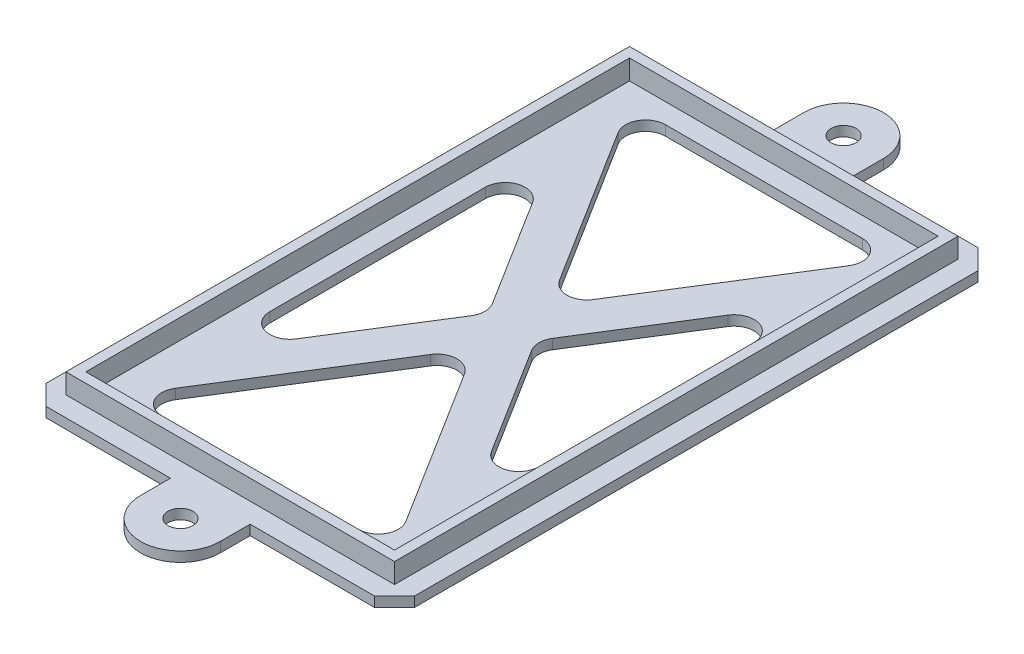
SolidWorks part; units mm, degrees
ref_plane "Front Plane" through (0, 0, 0) normal (0, 0, 1) x (1, 0, 0)
ref_plane "Top Plane" through (0, 0, 0) normal (0, 1, 0) x (1, 0, 0)
ref_plane "Right Plane" through (0, 0, 0) normal (1, 0, 0) x (0, 0, -1)
sketch "Sketch1" plane through (0, 0, 0) normal (0, 1, 0) x (1, 0, 0)
  line L8 (1.27, 1.27) -> (1.27, -70.612)
  line L9 (0, 0) -> (-39.37, 0)
  line L10 (0, 0) -> (0, -69.342)
  line L11 (0, -69.342) -> (-39.37, -69.342)
  line L12 (-39.37, 0) -> (-39.37, -69.342)
  line L13 (1.27, -70.612) -> (-40.64, -70.612)
  line L14 (-40.64, 1.27) -> (-40.64, -70.612)
  line L15 (1.27, 1.27) -> (-40.64, 1.27)
  dimension "D1" = 39.37
  dimension "D2" = 69.342
  dimension "D3" = 1.27
extrude "Boss-Extrude4" add sketch "Sketch1" along normal blind 2.54
sketch "Sketch5" plane through (0, 0, 0) normal (0, -1, 0) x (1, 0, 0)
  line L14 (-43.18, -3.81) -> (3.81, -3.81)
  line L15 (3.81, -3.81) -> (3.81, 73.152)
  line L16 (-43.18, 73.152) -> (-43.18, -3.81)
  line L17 (3.81, 73.152) -> (-43.18, 73.152)
  line L18 (-43.18, -3.81) -> (3.81, -3.81)
  line L19 (3.81, -3.81) -> (3.81, 73.152)
  line L20 (-43.18, 73.152) -> (-43.18, -3.81)
  line L21 (3.81, 73.152) -> (-43.18, 73.152)
  dimension "D1" = 2.54
extrude "Boss-Extrude5" add sketch "Sketch5" along normal blind 1.27
chamfer "Chamfer4" distance 2.54 angle 45 4 edges at (-43.18, -0.635, 73.152) (3.81, -0.635, 73.152) (3.81, -0.635, -3.81) (-43.18, -0.635, -3.81)
sketch "Sketch6" plane through (0, 0, 0) normal (0, 1, 0) x (1, 0, 0)
  line L0 (0, 0) -> (-39.37, 0) construction
  line L1 (-36.83, -2.54) -> (-2.54, -2.54)
  line L2 (-36.83, -12.1041) -> (-36.83, -57.2379)
  line L3 (-36.83, -66.802) -> (-2.54, -66.802)
  line L4 (-2.54, -12.1041) -> (-2.54, -57.2379)
  line L5 (0, -69.342) -> (0, 0) construction
  line L6 (-39.37, -69.342) -> (0, -69.342) construction
  line L7 (-39.37, 0) -> (-39.37, -69.342) construction
  line L8 (-36.83, -57.2379) -> (-22.6828, -34.671)
  line L9 (-2.54, -12.1041) -> (-16.6872, -34.671)
  line L10 (-36.83, -12.1041) -> (-22.6828, -34.671)
  line L11 (-36.83, -2.54) -> (-19.685, -29.889)
  line L12 (-19.685, -39.453) -> (-2.54, -66.802)
  line L13 (-16.6872, -34.671) -> (-2.54, -57.2379)
  line L14 (-19.685, -29.889) -> (-2.54, -2.54)
  line L15 (-19.685, -39.453) -> (-36.83, -66.802)
  line L16 (-40.64, -70.612) -> (1.27, -70.612) construction
  point P3 (-19.685, -70.612)
  point P24 (0, -34.671)
  dimension "D1" = 2.54
  dimension "D2" = 2.54
  dimension "D3" = 2.54
  dimension "D4" = 2.54
  dimension "D5" = 5.08
  dimension "D6" = 5.08
  dimension "D7" = 2.54
extrude "Cut-Extrude1" cut sketch "Sketch6" against normal blind 2.54
fillet "Fillet1" radius 2.54 12 edges at (-19.685, -0.635, 39.453) (-36.83, -0.635, 66.802) (-2.54, -0.635, 57.2379) (-2.54, -0.635, 12.1041) (-16.6872, -0.635, 34.671) (-22.6828, -0.635, 34.671) (-19.685, -0.635, 29.889) (-2.54, -0.635, 2.54) (-36.83, -0.635, 12.1041) (-2.54, -0.635, 66.802) (-36.83, -0.635, 57.2379) (-36.83, -0.635, 2.54)
sketch "Sketch7" plane through (0, 0, 0) normal (0, 1, 0) x (1, 0, 0)
  line L0 (-40.64, 3.81) -> (1.27, 3.81) construction
  line L1 (-14.605, 7.62) -> (-14.605, 3.81)
  line L2 (-14.605, 3.81) -> (-24.765, 3.81)
  line L3 (-24.765, 3.81) -> (-24.765, 7.62)
  line L4 (-996.19, -34.671) -> (49003.81, -34.671)
  line L5 (3.81, 1.27) -> (3.81, -70.612) construction
  line L6 (-24.765, -73.152) -> (-24.765, -76.962)
  line L7 (-14.605, -73.152) -> (-24.765, -73.152)
  line L8 (-14.605, -76.962) -> (-14.605, -73.152)
  circle A0 centre (-19.685, 7.62) radius 1.5875
  arc A1 (-14.605, 7.62) -> (-24.765, 7.62) centre (-19.685, 7.62) ccw
  arc A2 (-14.605, -76.962) -> (-24.765, -76.962) centre (-19.685, -76.962) cw
  circle A3 centre (-19.685, -76.962) radius 1.5875
  point P6 (-19.685, 3.81)
  point P14 (3.81, -34.671)
  dimension "D1" = 3.175
  dimension "D2" = 5.08
  dimension "D3" = 3.81
extrude "Boss-Extrude6" add sketch "Sketch7" against normal blind 1.27
